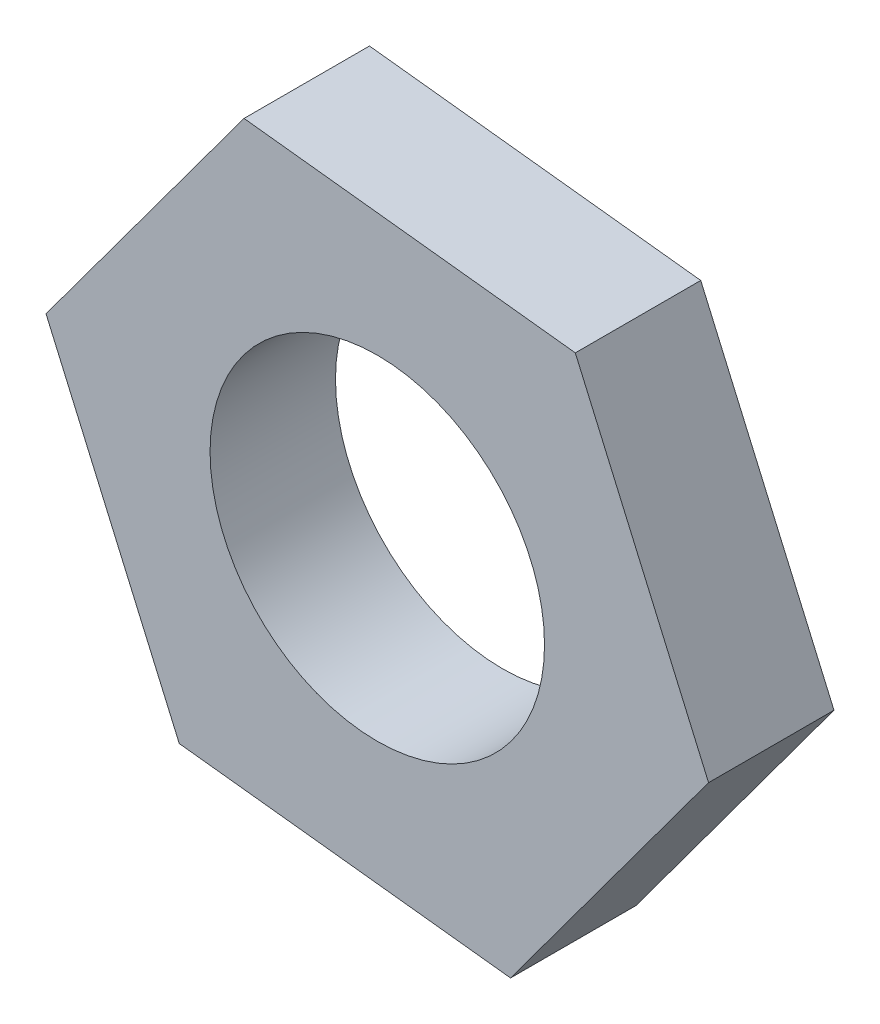
SolidWorks part; units mm, degrees
ref_plane "前视基准面" through (0, 0, 0) normal (0, 0, 1) x (1, 0, 0)
ref_plane "上视基准面" through (0, 0, 0) normal (0, 1, 0) x (1, 0, 0)
ref_plane "右视基准面" through (0, 0, 0) normal (1, 0, 0) x (0, 0, -1)
sketch "草图1" plane through (0, 0, 0) normal (0, 0, 1) x (1, 0, 0)
  line L0 (3.1872, -7.3094) -> (7.9237, -0.8946)
  line L1 (7.9237, -0.8946) -> (4.7366, 6.4149)
  line L2 (4.7366, 6.4149) -> (-3.1872, 7.3094)
  line L3 (-3.1872, 7.3094) -> (-7.9237, 0.8946)
  line L4 (-7.9237, 0.8946) -> (-4.7366, -6.4149)
  line L5 (-4.7366, -6.4149) -> (3.1872, -7.3094)
  circle A0 centre (0, 0) radius 4
  circle A1 centre (0, 0) radius 6.9057 construction
extrude "凸台-拉伸2" add sketch "草图1" along normal blind 3
